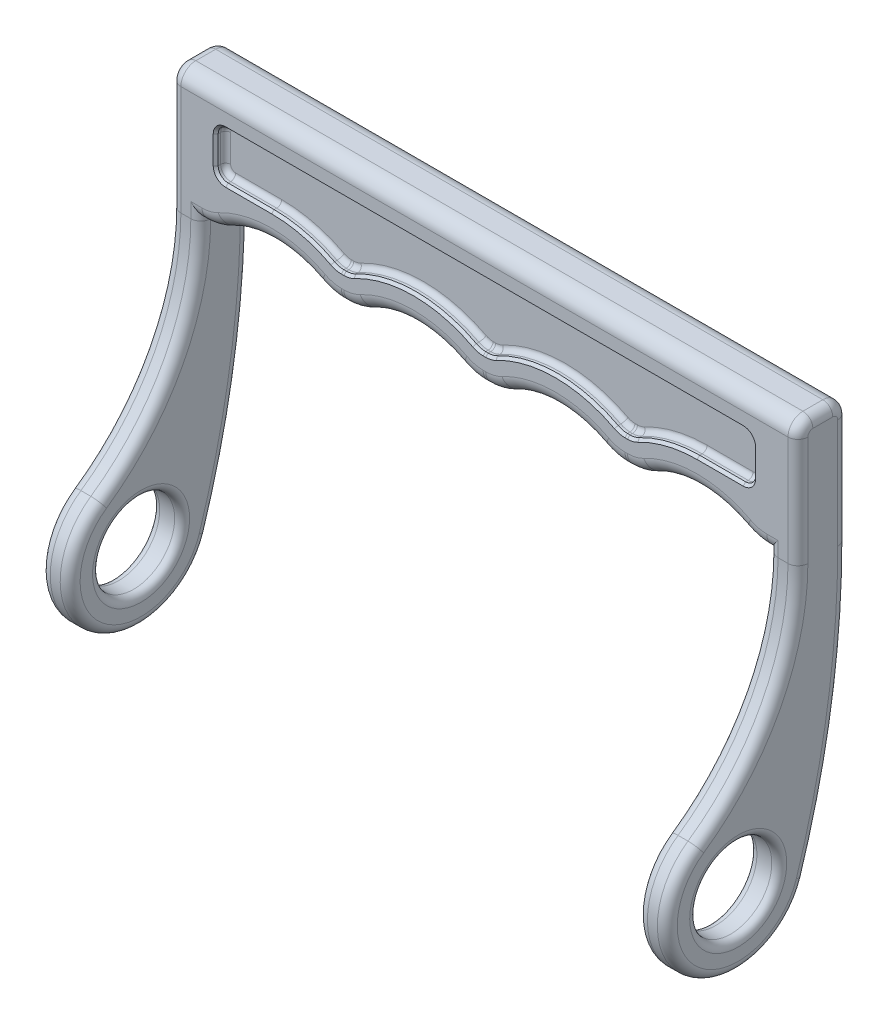
SolidWorks part; units mm, degrees
ref_plane "Front Plane" through (0, 0, 0) normal (0, 0, 1) x (1, 0, 0)
ref_plane "Top Plane" through (0, 0, 0) normal (0, 1, 0) x (1, 0, 0)
ref_plane "Right Plane" through (0, 0, 0) normal (1, 0, 0) x (0, 0, -1)
sketch "Sketch3" plane through (0, 0, 0) normal (0, 0, 1) x (1, 0, 0)
  line L1 (-57, -12.5) -> (57, -12.5)
  line L2 (-57, -12.5) -> (-57, 12.5)
  line L3 (-57, 12.5) -> (57, 12.5)
  line L4 (57, -12.5) -> (57, 12.5)
  line L5 (-57, -12.5) -> (57, 12.5) construction
  line L6 (-57, 12.5) -> (57, -12.5) construction
  point P0 (0, 0)
  dimension "D1" = 114
  dimension "D2" = 25
extrude "Boss-Extrude1" add sketch "Sketch3" along normal mid plane 10
sketch "Sketch4" plane through (0, 0, 5) normal (0, 0, 1) x (1, 0, 0)
  line L0 (-57, -12.5) -> (57, -12.5) construction
  line L1 (31.5, -12.5) -> (54, -12.5)
  line L2 (57, -12.5) -> (57, 12.5) construction
  line L3 (3, -12.5) -> (25.5, -12.5)
  line L4 (-25.5, -12.5) -> (-3, -12.5)
  line L5 (-54, -12.5) -> (-31.5, -12.5)
  line L6 (-57, 12.5) -> (-57, -12.5) construction
  arc A0 (31.5, -12.5) -> (54, -12.5) centre (42.75, -29.0359) cw
  arc A1 (3, -12.5) -> (25.5, -12.5) centre (14.25, -29.0359) cw
  arc A2 (-25.5, -12.5) -> (-3, -12.5) centre (-14.25, -29.0359) cw
  arc A3 (-54, -12.5) -> (-31.5, -12.5) centre (-42.75, -29.0359) cw
  point P7 (-50.8796, -12.5)
  dimension "D2" = 20
  dimension "D1" = 3
  dimension "D4" = 3
  dimension "D5" = 6
  dimension "D3" = 4
extrude "Cut-Extrude1" cut sketch "Sketch4" against normal through all
sketch "Sketch5" plane through (0, 0, 5) normal (0, 0, 1) x (1, 0, 0)
  line L23 (-54, -1.0359) -> (-54, 4.5)
  line L24 (-52, 6.5) -> (52, 6.5)
  line L25 (54, 4.5) -> (54, -1.0359)
  line L26 (29.7835, -6.5) -> (27.2165, -6.5)
  line L27 (1.2835, -6.5) -> (-1.2835, -6.5)
  line L28 (-27.2165, -6.5) -> (-29.7835, -6.5)
  line L29 (28.7556, -6.5) -> (28.2444, -6.5)
  line L30 (0.2556, -6.5) -> (-0.2556, -6.5)
  line L31 (-28.2444, -6.5) -> (-28.7556, -6.5)
  line L32 (-57, 12.5) -> (-57, -12.5) construction
  line L33 (57, 12.5) -> (-57, 12.5) construction
  line L34 (57, -12.5) -> (57, 12.5) construction
  line L35 (-42.75, -3.0359) -> (-52, -3.0359)
  line L36 (42.75, -3.0359) -> (52, -3.0359)
  arc A33 (42.75, -3.0359) -> (30.6215, -6.0381) centre (42.75, -29.0359) ccw
  arc A34 (52, -3.0359) -> (54, -1.0359) centre (52, -1.0359) ccw
  arc A35 (54, 4.5) -> (52, 6.5) centre (52, 4.5) ccw
  arc A36 (-54, -1.0359) -> (-52, -3.0359) centre (-52, -1.0359) ccw
  arc A37 (57.375, -7.5392) -> (29.7835, -6.5) centre (42.75, -29.0359) ccw
  arc A38 (27.2165, -6.5) -> (1.2835, -6.5) centre (14.25, -29.0359) ccw
  arc A39 (-1.2835, -6.5) -> (-27.2165, -6.5) centre (-14.25, -29.0359) ccw
  arc A40 (-29.7835, -6.5) -> (-57.375, -7.5392) centre (-42.75, -29.0359) ccw
  arc A41 (-52, 6.5) -> (-54, 4.5) centre (-52, 4.5) ccw
  arc A42 (26.3785, -6.0381) -> (2.1215, -6.0381) centre (14.25, -29.0359) ccw
  arc A43 (-2.1215, -6.0381) -> (-26.3785, -6.0381) centre (-14.25, -29.0359) ccw
  arc A44 (-30.6215, -6.0381) -> (-42.75, -3.0359) centre (-42.75, -29.0359) ccw
  arc A45 (30.6215, -6.0381) -> (28.7556, -6.5) centre (28.7556, -2.5) cw
  arc A46 (28.2444, -6.5) -> (26.3785, -6.0381) centre (28.2444, -2.5) cw
  arc A47 (2.1215, -6.0381) -> (0.2556, -6.5) centre (0.2556, -2.5) cw
  arc A48 (-0.2556, -6.5) -> (-2.1215, -6.0381) centre (-0.2556, -2.5) cw
  arc A49 (-26.3785, -6.0381) -> (-28.2444, -6.5) centre (-28.2444, -2.5) cw
  arc A50 (-28.7556, -6.5) -> (-30.6215, -6.0381) centre (-28.7556, -2.5) cw
  dimension "D5" = 2
  dimension "D6" = 4
  dimension "D2" = 3
  dimension "D3" = 6
  dimension "D4" = 3
  dimension "D1" = 6
extrude "Cut-Extrude2" cut sketch "Sketch5" against normal blind 2
mirror "Mirror1" about plane through (0, 0, 0) normal (0, 0, 1) of "Cut-Extrude2"
sketch "Sketch6" plane through (57, 0, 0) normal (1, 0, 0) x (0, 0, -1)
  line L1 (-5, -12.5) -> (5, -12.5) construction
  line L4 (5, -12.5) -> (5, 12.5)
  line L5 (5, 12.5) -> (-5, 12.5)
  line L6 (-5, 12.5) -> (-5, -12.5)
  line L7 (-5, -12.5) -> (5, -12.5)
  line L8 (5, -12.5) -> (5, 12.5)
  line L9 (5, 12.5) -> (-5, 12.5)
  line L10 (-5, 12.5) -> (-5, -12.5)
  circle A0 centre (-17, -62.5) radius 8.25
  arc A1 (-25.092, -50.7705) -> (-3.4186, -66.8139) centre (-17, -62.5) ccw
  arc A2 (-5, -12.5) -> (-25.092, -50.7705) centre (-51.494, -12.5) cw
  arc A3 (5, -12.5) -> (-3.4186, -66.8139) centre (-174.4153, -12.5) cw
  point P12 (0, 0)
  point P13 (0, 0)
  point P14 (-8.0411, -73.5815)
  point P15 (0, 0)
  point P16 (0, 0)
  dimension "D4" = 16.5
  dimension "D5" = 14.25
  dimension "D2" = 12
  dimension "D3" = 50
  dimension "D1" = 0
extrude "Boss-Extrude2" add sketch "Sketch6" along normal blind 6
mirror "Mirror2" about plane through (0, 0, 0) normal (1, 0, 0) of "Boss-Extrude2"
fillet "Fillet1" radius 10 8 edges at (31.5, -12.5, 0) (54, -12.5, 0) (3, -12.5, 0) (25.5, -12.5, 0) (-25.5, -12.5, 0) (-3, -12.5, 0) (-54, -12.5, 0) (-31.5, -12.5, 0)
fillet "Fillet2" radius 3 36 edges at (56.8722, -12.5, -5) (54.3416, -12.207, -5) (42.75, -9.0359, -5) (31.1584, -12.207, -5) (28.5, -12.5, -5) (25.8416, -12.207, -5) (14.25, -9.0359, -5) (2.6584, -12.207, -5) (0, -12.5, -5) (-2.6584, -12.207, -5) (-56.8722, -12.5, -5) (-54.3416, -12.207, -5) (-42.75, -9.0359, -5) (-31.1584, -12.207, -5) (-28.5, -12.5, -5) (-25.8416, -12.207, -5) (56.8722, -12.5, 5) (54.3416, -12.207, 5) (42.75, -9.0359, 5) (31.1584, -12.207, 5) (28.5, -12.5, 5) (25.8416, -12.207, 5) (14.25, -9.0359, 5) (2.6584, -12.207, 5) (0, -12.5, 5) (-2.6584, -12.207, 5) (-56.8722, -12.5, 5) (-54.3416, -12.207, 5) (-42.75, -9.0359, 5) (-31.1584, -12.207, 5) (-28.5, -12.5, 5) (-25.8416, -12.207, 5) (-14.25, -9.0359, -5) (0, 12.5, -5) (0, 12.5, 5) (-14.25, -9.0359, 5)
fillet "Fillet3" radius 2 26 edges at (63, -34.112, 10.3283) (63, -1.5, 5) (63, 11.6213, 4.1213) (63, 12.5, 0) (63, 11.6213, -4.1213) (63, -1.5, -5) (63, -39.9812, -2.8828) (57, -11, 5) (57, -34.112, 10.3283) (57, -11, -5) (57, -39.9812, -2.8828) (-63, -34.112, 10.3283) (-63, -1.5, 5) (-63, 11.6213, 4.1213) (-63, 12.5, 0) (-63, 11.6213, -4.1213) (-63, -1.5, -5) (-63, -39.9812, -2.8828) (-57, -11, 5) (-57, -34.112, 10.3283) (-57, -11, -5) (-57, -39.9812, -2.8828) (63, -73.9535, 25.4783) (57, -73.9535, 25.4783) (-63, -73.9535, 25.4783) (-57, -73.9535, 25.4783)
fillet "Fillet4" radius 1.5 4 edges at (57, -62.5, 8.75) (63, -62.5, 8.75) (-57, -62.5, 8.75) (-63, -62.5, 8.75)
fillet "Fillet5" radius 1 22 edges at (47.375, -3.0359, 3) (36.5027, -3.7976, 3) (29.7167, -6.3828, 3) (28.5, -6.5, 3) (27.2833, -6.3828, 3) (14.25, -3.0359, 3) (1.2167, -6.3828, 3) (0, -6.5, 3) (-1.2167, -6.3828, 3) (-14.25, -3.0359, 3) (-27.2833, -6.3828, 3) (-28.5, -6.5, 3) (-29.7167, -6.3828, 3) (-36.5027, -3.7976, 3) (-47.375, -3.0359, 3) (-53.4142, -2.4502, 3) (-54, 1.732, 3) (-53.4142, 5.9142, 3) (0, 6.5, 3) (53.4142, 5.9142, 3) (54, 1.732, 3) (53.4142, -2.4502, 3)
fillet "Fillet6" radius 1 22 edges at (54, 1.732, -3) (53.4142, 5.9142, -3) (0, 6.5, -3) (-53.4142, 5.9142, -3) (-54, 1.732, -3) (-53.4142, -2.4502, -3) (-47.375, -3.0359, -3) (-36.5027, -3.7976, -3) (-29.7167, -6.3828, -3) (-28.5, -6.5, -3) (-27.2833, -6.3828, -3) (-14.25, -3.0359, -3) (-1.2167, -6.3828, -3) (0, -6.5, -3) (1.2167, -6.3828, -3) (14.25, -3.0359, -3) (27.2833, -6.3828, -3) (28.5, -6.5, -3) (29.7167, -6.3828, -3) (36.5027, -3.7976, -3) (47.375, -3.0359, -3) (53.4142, -2.4502, -3)
chamfer "Chamfer1" distance 0.5 angle 45 44 edges at (-29.7167, -6.3828, 5) (-28.5, -6.5, 5) (-36.5027, -3.7976, 5) (-27.2833, -6.3828, 5) (-47.375, -3.0359, 5) (-14.25, -3.0359, 5) (-53.4142, -2.4502, 5) (-1.2167, -6.3828, 5) (-54, 1.732, 5) (0, -6.5, 5) (-53.4142, 5.9142, 5) (1.2167, -6.3828, 5) (0, 6.5, 5) (14.25, -3.0359, 5) (53.4142, 5.9142, 5) (27.2833, -6.3828, 5) (54, 1.732, 5) (28.5, -6.5, 5) (53.4142, -2.4502, 5) (29.7167, -6.3828, 5) (47.375, -3.0359, 5) (36.5027, -3.7976, 5) (-54, 1.732, -5) (-53.4142, -2.4502, -5) (-53.4142, 5.9142, -5) (-47.375, -3.0359, -5) (0, 6.5, -5) (-36.5027, -3.7976, -5) (53.4142, 5.9142, -5) (-29.7167, -6.3828, -5) (54, 1.732, -5) (-28.5, -6.5, -5) (53.4142, -2.4502, -5) (-27.2833, -6.3828, -5) (47.375, -3.0359, -5) (-14.25, -3.0359, -5) (36.5027, -3.7976, -5) (-1.2167, -6.3828, -5) (29.7167, -6.3828, -5) (0, -6.5, -5) (28.5, -6.5, -5) (1.2167, -6.3828, -5) (27.2833, -6.3828, -5) (14.25, -3.0359, -5)
